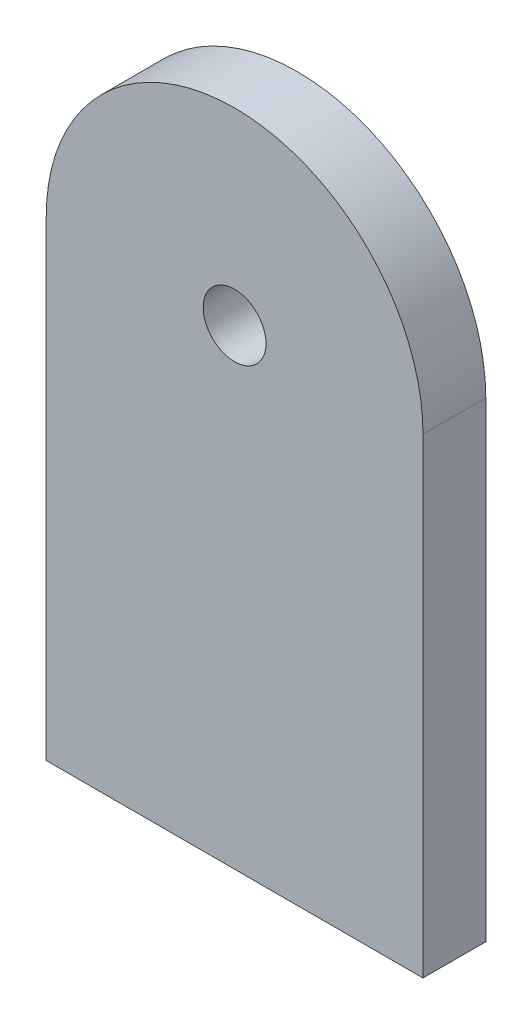
SolidWorks part; units mm, degrees
ref_plane "Alzado" through (0, 0, 0) normal (0, 0, 1) x (1, 0, 0)
ref_plane "Planta" through (0, 0, 0) normal (0, 1, 0) x (1, 0, 0)
ref_plane "Vista lateral" through (0, 0, 0) normal (1, 0, 0) x (0, 0, -1)
sketch "Croquis1" plane through (0, 0, 0) normal (0, 0, 1) x (1, 0, 0)
  line L1 (9.5, -75) -> (-30, -75)
  line L2 (-30, -75) -> (-30, 0)
  line L3 (9.5, -75) -> (30, -75)
  line L4 (30, -75) -> (30, 0)
  arc A0 (30, 0) -> (-30, 0) centre (0, 0) ccw
  circle A1 centre (0, 0) radius 5
extrude "Saliente-Extruir1" add sketch "Croquis1" along normal blind 10 contours A0 L2 L1 L3 L4 | A1
